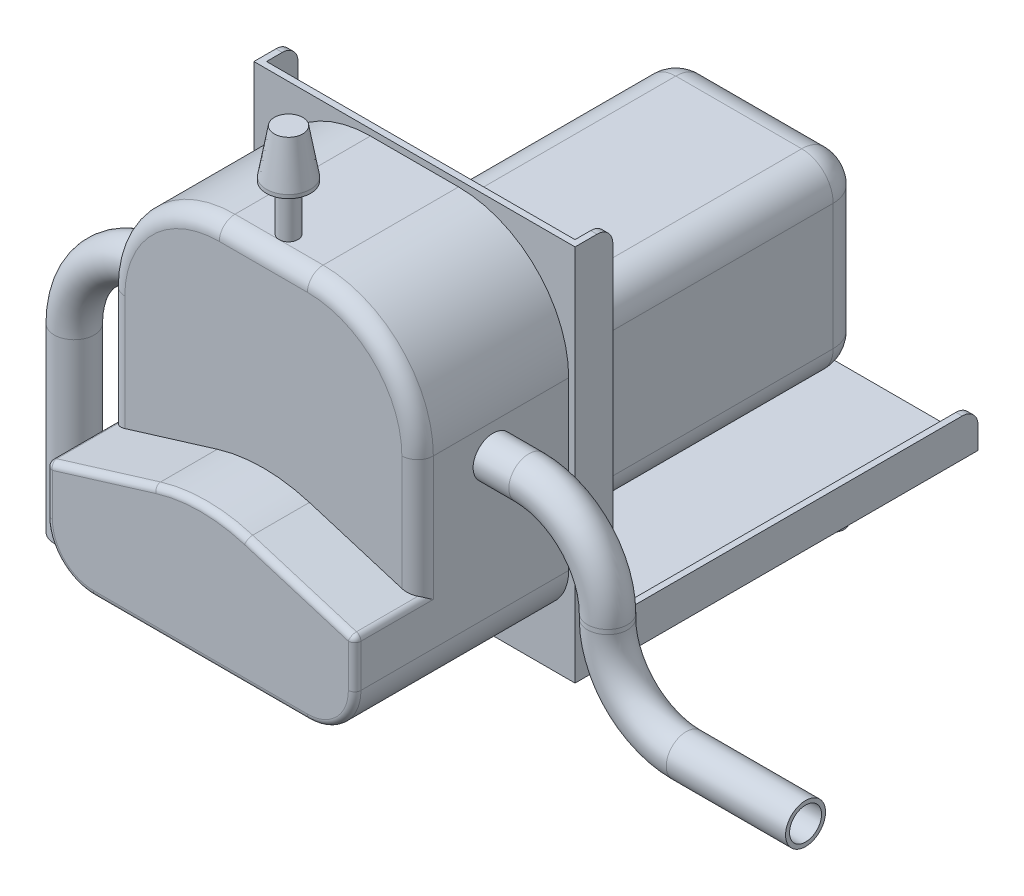
SolidWorks part; units mm, degrees
ref_plane "Front Plane" through (0, 0, 0) normal (0, 0, 1) x (1, 0, 0)
ref_plane "Top Plane" through (0, 0, 0) normal (0, 1, 0) x (1, 0, 0)
ref_plane "Right Plane" through (0, 0, 0) normal (1, 0, 0) x (0, 0, -1)
sketch "Sketch1" plane through (0, 0, 0) normal (0, 0, 1) x (1, 0, 0)
  line L1 (-51, -60) -> (51, -60)
  line L2 (-51, -60) -> (-51, 60)
  line L3 (-51, 60) -> (51, 60)
  line L4 (51, -60) -> (51, 60)
  line L5 (-51, -60) -> (51, 60) construction
  line L6 (-51, 60) -> (51, -60) construction
  point P0 (0, 0)
  dimension "D1" = 102
  dimension "D2" = 120
extrude "Boss-Extrude1" add sketch "Sketch1" along normal blind 2
sketch "Sketch2" plane through (0, -60, 0) normal (0, -1, 0) x (1, 0, 0)
  line L0 (51, 2) -> (51, 0) construction
  line L1 (-51, 2) -> (51, 2)
  line L2 (-51, 2) -> (-51, -126)
  line L3 (-51, -126) -> (51, -126)
  line L4 (51, 2) -> (51, -126)
  dimension "D1" = 128
extrude "Boss-Extrude2" add sketch "Sketch2" against normal blind 2
sketch "Sketch3" plane through (51, 0, 0) normal (1, 0, 0) x (0, 0, -1)
  line L1 (-2, 60) -> (10, 60)
  line L2 (-2, 60) -> (-2, -48)
  line L4 (10, 60) -> (10, -48)
  line L6 (126, -60) -> (-2, -60)
  line L7 (126, -60) -> (126, -48)
  line L8 (126, -48) -> (10, -48)
  line L9 (-2, -60) -> (-2, -48)
  dimension "D1" = 12
extrude "Boss-Extrude3" add sketch "Sketch3" against normal blind 2
mirror "Mirror1" about plane through (0, 0, 0) normal (1, 0, 0) of "Boss-Extrude3"
fillet "Fillet1" radius 5 4 edges at (-50, -48, -126) (50, -48, -126) (-50, 60, -10) (50, 60, -10)
sketch "Sketch5" plane through (0, -60, 0) normal (0, -1, 0) x (1, 0, 0)
  line L0 (-51, 2) -> (51, 2) construction
  line L1 (-42, -13) -> (42, -13) construction
  circle A0 centre (-42, -13) radius 3.5
  circle A1 centre (42, -13) radius 3.5
  circle A2 centre (-42, -89) radius 3.5
  circle A3 centre (42, -89) radius 3.5
  circle A4 centre (-42, -13) radius 2.5
  circle A5 centre (42, -13) radius 2.5
  circle A6 centre (42, -89) radius 2.5
  circle A7 centre (-42, -89) radius 2.5
  point P8 (0, -13)
  dimension "D2" = 7
  dimension "D5" = 5
  dimension "D1" = 76
  dimension "D3" = 15
  dimension "D4" = 84
extrude "Boss-Extrude4" add sketch "Sketch5" along normal offset from surface (6 mm away) 126 up to face at (0, 60, -2)
sketch "Sketch4" plane through (0, 0, 2) normal (0, 0, 1) x (1, 0, 0)
  line L0 (-51, 60) -> (-51, -60) construction
  line L1 (-49, -45) -> (49, -45)
  line L2 (-49, -45) -> (-49, 58)
  line L3 (-49, 58) -> (49, 58)
  line L4 (49, -45) -> (49, 58)
  line L5 (-49, -45) -> (49, 58) construction
  line L6 (-49, 58) -> (49, -45) construction
  line L7 (51, -60) -> (51, 60) construction
  line L8 (-45.5, -66) -> (-38.5, -66) construction
  line L9 (51, 60) -> (-51, 60) construction
  point P0 (0, 6.5)
  dimension "D1" = 2
  dimension "D2" = 2
  dimension "D3" = 21
  dimension "D4" = 2
extrude "Boss-Extrude5" add sketch "Sketch4" along normal offset from surface (68 mm away) 196 up to face at (0, -56, -126)
fillet "Fillet2" radius 35 2 edges at (-49, 58, 36) (49, 58, 36)
fillet "Fillet3" radius 15 2 edges at (49, -45, 36) (-49, -45, 36)
sketch "Sketch6" plane through (0, 0, 70) normal (0, 0, 1) x (1, 0, 0)
  line L0 (-49, -15) -> (-14.6357, -4.4803)
  line L1 (14.6357, -4.4803) -> (49, -15)
  line L4 (-34, -45) -> (34, -45)
  line L5 (49, -30) -> (49, 23)
  line L6 (14, 58) -> (-14, 58)
  line L7 (-49, 23) -> (-49, -30)
  line L9 (49, -15) -> (49, 23)
  line L10 (14, 58) -> (-14, 58)
  line L11 (-49, 23) -> (-49, -15)
  arc A0 (-14.6357, -4.4803) -> (14.6357, -4.4803) centre (0, -52.2903) cw
  arc A4 (34, -45) -> (49, -30) centre (34, -30) ccw
  arc A5 (49, 23) -> (14, 58) centre (14, 23) ccw
  arc A6 (-14, 58) -> (-49, 23) centre (-14, 23) ccw
  arc A7 (-49, -30) -> (-34, -45) centre (-34, -30) ccw
  arc A9 (49, 23) -> (14, 58) centre (14, 23) ccw
  arc A10 (-14, 58) -> (-49, 23) centre (-14, 23) ccw
  point P18 (0, 0)
  dimension "D3" = 50
  dimension "D2" = 73
  dimension "D1" = 0
extrude "Cut-Extrude1" cut sketch "Sketch6" against normal blind 20
fillet "Fillet4" radius 5 5 edges at (49, 4, 50) (38.7487, 47.7487, 50) (-49, 4, 50) (-38.7487, 47.7487, 50) (0, 58, 50)
fillet "Fillet5" radius 2 10 edges at (-31.8179, -9.7402, 70) (31.8179, -9.7402, 70) (-49, -15, 57.5) (49, -15, 57.5) (0, -2.2903, 70) (-49, -22.5, 70) (-44.6066, -40.6066, 70) (0, -45, 70) (44.6066, -40.6066, 70) (49, -22.5, 70)
sketch "Sketch8" plane through (0, 0, 0) normal (0, 0, -1) x (-1, 0, 0)
  line L0 (51, -60) -> (-51, -60) construction
  line L1 (-30, -40) -> (30, -40)
  line L2 (-30, -40) -> (-30, 20)
  line L3 (-30, 20) -> (30, 20)
  line L4 (30, -40) -> (30, 20)
  line L5 (-30, -40) -> (30, 20) construction
  line L6 (-30, 20) -> (30, -40) construction
  point P0 (0, -10)
  dimension "D1" = 60
  dimension "D2" = 60
  dimension "D3" = 50
extrude "Boss-Extrude6" add sketch "Sketch8" along normal offset from surface (111 mm away) 15 up to face at (0, -56, -126)
fillet "Fillet6" radius 10 8 edges at (30, -10, -111) (0, 20, -111) (-30, -10, -111) (0, -40, -111) (-30, -40, -55.5) (-30, 20, -55.5) (30, -40, -55.5) (30, 20, -55.5)
sketch "Sketch10" plane through (0, 58, 0) normal (0, 1, 0) x (1, 0, 0)
  line L0 (51, -2) -> (-51, -2) construction
  circle A0 centre (0, -42) radius 3
  dimension "D1" = 6
  dimension "D2" = 40
extrude "Boss-Extrude7" add sketch "Sketch10" along normal blind 29.85
sketch "Sketch11" plane through (0, 87.85, 0) normal (0, 1, 0) x (1, 0, 0)
  circle A0 centre (0, -42) radius 7
  dimension "D1" = 14
extrude "Boss-Extrude8" add sketch "Sketch11" against normal blind 15.15
chamfer "Chamfer1" distance 14 angle 10 1 edges at (0, 87.85, 49)
sketch "Sketch15" plane through (0, 0, 2) normal (0, 0, 1) x (1, 0, 0)
  line L5 (14.6357, -4.4803) -> (44, -13.4694)
  line L6 (44, -13.4694) -> (44, 23)
  line L7 (14, 53) -> (-14, 53)
  line L8 (-44, 23) -> (-44, -13.4694)
  line L9 (-44, -13.4694) -> (-14.6357, -4.4803)
  line L11 (44, -13.4694) -> (44, 23)
  line L12 (14, 53) -> (-14, 53)
  line L13 (-44, 23) -> (-44, -13.4694)
  line L15 (-44, -16.4794) -> (-44, -13.4694)
  line L16 (34, -40) -> (-34, -40)
  line L17 (-44, -30) -> (-44, -16.4794)
  line L18 (34, -40) -> (-34, -40)
  line L19 (-44, -30) -> (-44, -16.4794)
  line L20 (44, -30) -> (44, -16.4794)
  line L21 (44, -30) -> (44, -16.4794)
  line L22 (44, -16.4794) -> (44, -13.4694)
  arc A3 (44, 23) -> (14, 53) centre (14, 23) ccw
  arc A4 (-14, 53) -> (-44, 23) centre (-14, 23) ccw
  arc A5 (14.6357, -4.4803) -> (-14.6357, -4.4803) centre (0, -52.2903) ccw
  arc A6 (44, 23) -> (14, 53) centre (14, 23) ccw
  arc A7 (-14, 53) -> (-44, 23) centre (-14, 23) ccw
  arc A9 (-44, -30) -> (-34, -40) centre (-34, -30) ccw
  arc A10 (-44, -30) -> (-34, -40) centre (-34, -30) ccw
  arc A13 (34, -40) -> (44, -30) centre (34, -30) ccw
  arc A14 (34, -40) -> (44, -30) centre (34, -30) ccw
  dimension "D1" = 0
  dimension "D2" = 5
  dimension "D3" = 5
extrude "Cut-Extrude2" cut sketch "Sketch15" along normal offset from surface (38 mm away) 10 up to face at (0, 16.3396, 50)
sketch "Sketch12" plane through (-49, 0, 0) normal (-1, 0, 0) x (0, 0, 1)
  circle A0 centre (26.0216, 13.4287) radius 6.35
  circle A1 centre (26.0216, 13.4287) radius 5.08
  point P3 (26.0216, 13.4287)
  dimension "D1" = 12.7
  dimension "D2" = 10.16
sketch "Sketch13" plane through (0, 0, 50) normal (0, 0, 1) x (1, 0, 0)
  line L4 (-54.0471, 13.4287) -> (60.3462, 13.4287)
  line L5 (85.3462, -11.5713) -> (85.3462, -12.9961)
  line L6 (110.3462, -37.9961) -> (148.2448, -37.9961)
  line L7 (-84.0471, -16.5713) -> (-84.0471, -73.9381)
  arc A0 (-54.0471, 13.4287) -> (-84.0471, -16.5713) centre (-54.0471, -16.5713) ccw
  arc A1 (85.3462, -12.9961) -> (110.3462, -37.9961) centre (110.3462, -12.9961) ccw
  arc A2 (60.3462, 13.4287) -> (85.3462, -11.5713) centre (60.3462, -11.5713) cw
  dimension "D1" = 30
  dimension "D2" = 25
sweep "Sweep1" add profiles "Sketch12" path "Sketch13"
